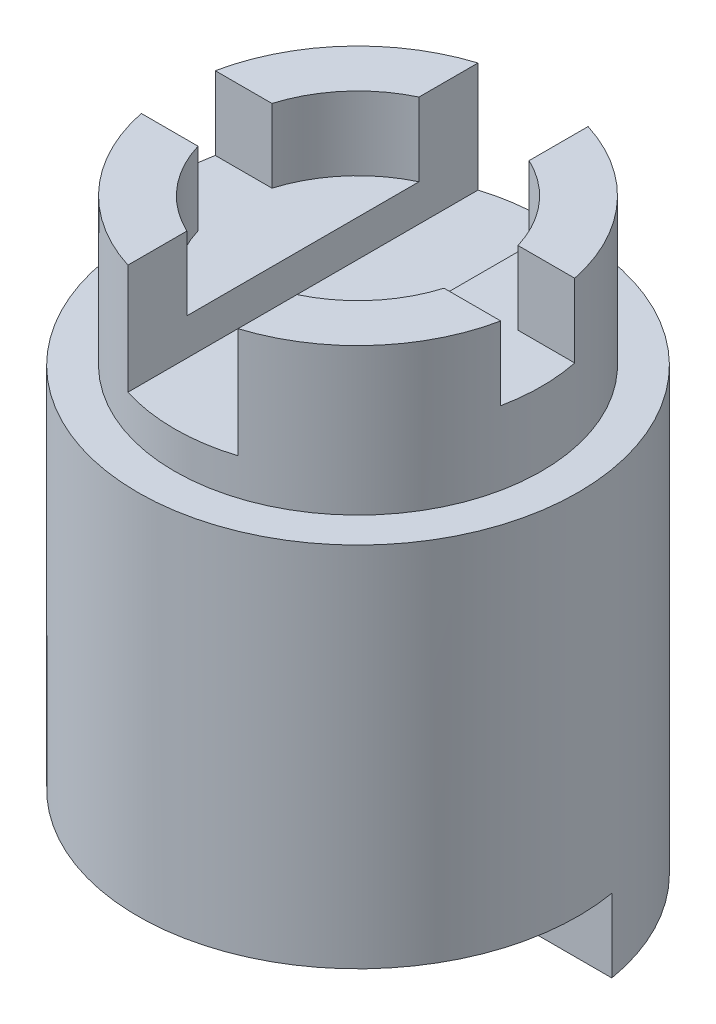
SolidWorks part; units mm, degrees
ref_plane "Front Plane" through (0, 0, 0) normal (0, 0, 1) x (1, 0, 0)
ref_plane "Top Plane" through (0, 0, 0) normal (0, 1, 0) x (1, 0, 0)
ref_plane "Right Plane" through (0, 0, 0) normal (1, 0, 0) x (0, 0, -1)
sketch "Sketch1" plane through (0, 0, 0) normal (0, 1, 0) x (1, 0, 0)
  circle A0 centre (0, 0) radius 19.05
  dimension "D1" = 38.1
extrude "1.5\" diameter 2\" tall cylinder" add sketch "Sketch1" along normal blind 50.8
sketch "Sketch2" plane through (0, 50.8, 0) normal (0, 1, 0) x (1, 0, 0)
  circle A0 centre (0, 0) radius 15.875
  circle A1 centre (0, 0) radius 19.05
  circle A2 centre (0, 0) radius 19.05 construction
  dimension "D1" = 31.75
extrude "1.25\" diameter x .5\" cylinder cut" cut sketch "Sketch2" against normal blind 12.7
sketch "Sketch3" plane through (0, 50.8, 0) normal (0, 1, 0) x (1, 0, 0)
  circle A0 centre (0, 0) radius 11.1125
  dimension "D1" = 22.225
extrude "Cut-Extrude2" cut sketch "Sketch3" against normal blind 6.35
sketch "Sketch4" plane through (0, 50.8, 0) normal (0, 1, 0) x (1, 0, 0)
  line L1 (-4.7625, 19.05) -> (4.7625, 19.05)
  line L2 (-4.7625, 19.05) -> (-4.7625, -19.05)
  line L3 (-4.7625, -19.05) -> (4.7625, -19.05)
  line L4 (4.7625, 19.05) -> (4.7625, -19.05)
  circle A0 centre (0, 0) radius 19.05 construction
  point P4 (0, 19.05)
  dimension "D1" = 9.525
extrude "Cut-Extrude3" cut sketch "Sketch4" against normal blind 9.525
sketch "Sketch5" plane through (0, 50.8, 0) normal (0, 1, 0) x (1, 0, 0)
  line L1 (-19.05, 3.2004) -> (19.05, 3.2004)
  line L2 (-19.05, 3.2004) -> (-19.05, -3.2004)
  line L3 (-19.05, -3.2004) -> (19.05, -3.2004)
  line L4 (19.05, 3.2004) -> (19.05, -3.2004)
  circle A0 centre (0, 0) radius 19.05 construction
  point P6 (-19.05, 0)
  dimension "D1" = 6.4008
extrude "Cut-Extrude4" cut sketch "Sketch5" against normal blind 6.35
sketch "Sketch11" plane through (0, 0, 0) normal (0, -1, 0) x (-1, 0, 0)
  circle A0 centre (0, 0) radius 9.525
  dimension "D1" = 19.05
extrude "Cut-Extrude5" cut sketch "Sketch11" against normal blind 6.35
sketch "Sketch12" plane through (0, 0, 0) normal (0, -1, 0) x (1, 0, 0)
  line L1 (-3.2004, 0) -> (3.2004, 0)
  line L2 (-3.2004, 0) -> (-3.2004, -19.05)
  line L3 (-3.2004, -19.05) -> (3.2004, -19.05)
  line L4 (3.2004, 0) -> (3.2004, -19.05)
  circle A0 centre (0, 0) radius 19.05 construction
  point P4 (0, 0)
  dimension "D1" = 6.4008
extrude "Cut-Extrude6" cut sketch "Sketch12" against normal blind 6.35
sketch "Sketch13" plane through (0, 0, 0) normal (0, -1, 0) x (1, 0, 0)
  line L1 (-19.05, -3.175) -> (19.05, -3.175)
  line L2 (-19.05, -3.175) -> (-19.05, 19.05)
  line L3 (-19.05, 19.05) -> (19.05, 19.05)
  line L4 (19.05, -3.175) -> (19.05, 19.05)
  arc A0 (3.2004, -18.7792) -> (-3.2004, -18.7792) centre (0, 0) ccw construction
  dimension "D1" = 3.175
extrude "Cut-Extrude7" cut sketch "Sketch13" against normal blind 6.35
